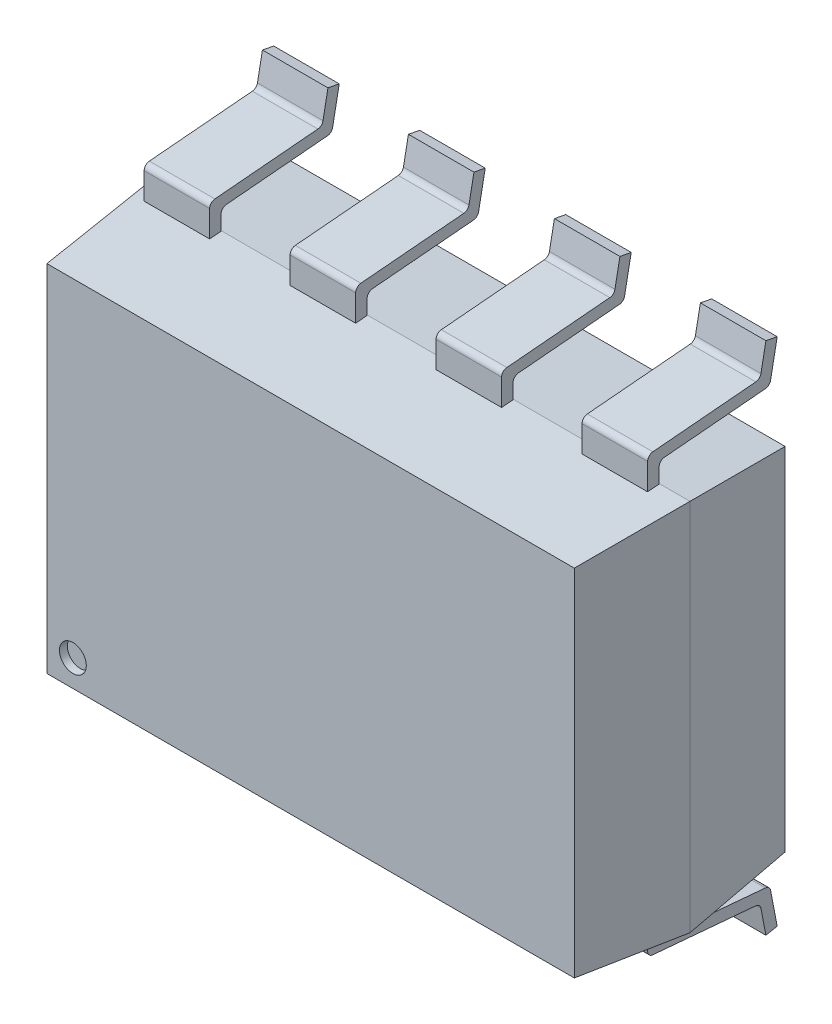
SolidWorks part; units mm, degrees
ref_plane "Front Plane" through (0, 0, 0) normal (0, 0, 1) x (1, 0, 0)
ref_plane "Top Plane" through (0, 0, 0) normal (0, 1, 0) x (1, 0, 0)
ref_plane "Right Plane" through (0, 0, 0) normal (1, 0, 0) x (0, 0, -1)
sketch "Sketch1" plane through (0, 0, 0) normal (0, 0, 1) x (1, 0, 0)
  line L1 (0, 0) -> (9.5, 0)
  line L2 (0, 0) -> (0, 6.5)
  line L3 (0, 6.5) -> (9.5, 6.5)
  line L4 (9.5, 0) -> (9.5, 6.5)
  dimension "D1" = 9.5
  dimension "D2" = 6.5
extrude "Boss-Extrude1" add sketch "Sketch1" along normal blind 1.85 draft 5
sketch "Sketch2" plane through (0, 0, 0) normal (0, 0, -1) x (-1, 0, 0)
  line L1 (-9.5, 6.5) -> (0, 6.5)
  line L2 (-9.5, 6.5) -> (-9.5, 0)
  line L3 (-9.5, 0) -> (0, 0)
  line L4 (0, 6.5) -> (0, 0)
extrude "Boss-Extrude2" add sketch "Sketch2" along normal blind 1.85 draft 6 separate body
sketch "Sketch3" plane through (0, 0, 1.85) normal (0, 0, 1) x (1, 0, 0)
  circle A0 centre (0.6138, 0.6221) radius 0.2336
extrude "Cut-Extrude1" cut sketch "Sketch3" against normal blind 0.127 draft 5
ref_plane "Plane1" through (0.78, 0, 0) normal (1, 0, 0) x (0, 0, -1)
sketch "Sketch4" plane through (0.78, 0, 0) normal (1, 0, 0) x (0, 0, -1)
  line L0 (-0.1068, 0.2204) -> (-0.1068, -0.44)
  line L1 (-0.1068, -0.44) -> (1.8349, -0.6108)
  line L2 (1.8349, -0.6108) -> (1.95, -1.2108)
  line L3 (1.85, 6.3056) -> (1.85, 0.1944) construction
  point P7 (1.7013, -0.44)
  point P8 (0, 0)
  point P9 (1.7363, -0.44)
  point P10 (0, 0)
  point P11 (0, 0)
  point P12 (0, 0.2204)
  point P13 (0, 0)
  point P14 (0, 0)
  point P15 (-0.1068, -0.44)
  point P16 (1.95, -1.2132)
  point P17 (1.7764, -0.6289)
  point P18 (1.95, -1.1968)
  point P19 (1.7269, -0.6043)
  point P20 (1.8349, -0.6108)
  dimension "D1" = 0.6
  dimension "D4" = 0.1
extrude "Extrude-Thin1" add sketch "Sketch4" along normal mid plane 1.14 separate body thin
pattern_linear "LPattern4" count 4 spacing 2.54 along (1, 0, 0) of "Extrude-Thin1"
fillet "Fillet1" radius 0.1 4 edges at (0.78, -0.7038, -1.7509) (0.78, -0.5178, -1.9188) (0.78, -0.3484, 0.0068) (0.78, -0.5316, 0.2068)
ref_plane "Plane3" through (0, 3.25, 0) normal (0, 1, 0) x (1, 0, 0)
fillet "Fillet2" radius 0.1 4 edges at (3.32, -0.5178, -1.9188) (3.32, -0.3484, 0.0068) (3.32, -0.7038, -1.7509) (3.32, -0.5316, 0.2068)
fillet "Fillet3" radius 0.1 4 edges at (5.86, -0.7038, -1.7509) (5.86, -0.5316, 0.2068) (5.86, -0.5178, -1.9188) (5.86, -0.3484, 0.0068)
fillet "Fillet4" radius 0.1 4 edges at (8.4, -0.5178, -1.9188) (8.4, -0.3484, 0.0068) (8.4, -0.7038, -1.7509) (8.4, -0.5316, 0.2068)
mirror "Mirror3" about plane through (0, 3.25, 0) normal (0, 1, 0) of "Extrude-Thin1", "Fillet1", "Fillet3", "Fillet2", "LPattern4", "Fillet4"
